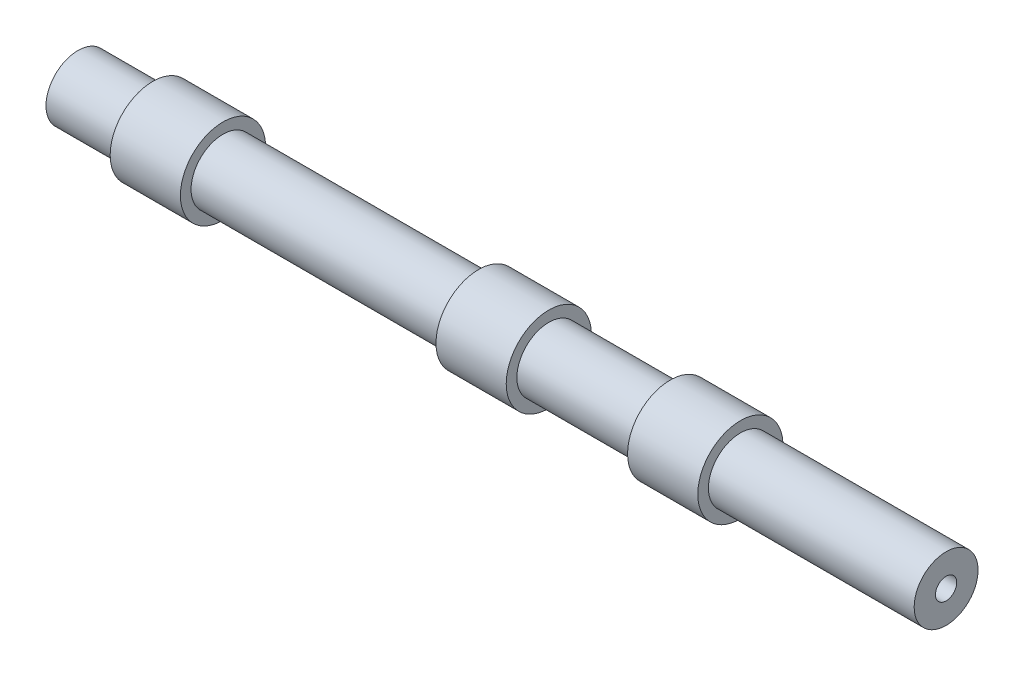
SolidWorks part; units mm, degrees
ref_plane "Front Plane" through (0, 0, 0) normal (0, 0, 1) x (1, 0, 0)
ref_plane "Top Plane" through (0, 0, 0) normal (0, 1, 0) x (1, 0, 0)
ref_plane "Right Plane" through (0, 0, 0) normal (1, 0, 0) x (0, 0, -1)
sketch "Sketch1" plane through (0, 0, 0) normal (0, 0, 1) x (1, 0, 0)
  line L0 (-102.2798, 0) -> (102.2798, 0) construction
  line L1 (-102.2798, 15) -> (-67.1503, 15)
  line L2 (-67.1503, 15) -> (-67.1503, 20)
  line L3 (-67.1503, 20) -> (-34.1803, 20)
  line L4 (-34.1803, 20) -> (-34.1803, 15)
  line L5 (-34.1803, 15) -> (85.8197, 15)
  line L6 (85.8197, 15) -> (85.8197, 20)
  line L7 (85.8197, 20) -> (118.7897, 20)
  line L8 (118.7897, 20) -> (118.7897, 15)
  line L9 (118.7897, 15) -> (175.7597, 15)
  line L10 (175.7597, 15) -> (175.7597, 20)
  line L11 (175.7597, 20) -> (208.7297, 20)
  line L12 (208.7297, 20) -> (208.7297, 15)
  line L13 (208.7297, 15) -> (218.2116, 15)
  line L14 (218.2116, 15) -> (305.3148, 15)
  point P4 (0, 0)
  dimension "D1" = 15
  dimension "D2" = 20
  dimension "D3" = 15
  dimension "D4" = 32.97
  dimension "D5" = 120
  dimension "D6" = 32.97
  dimension "D7" = 56.97
  dimension "D8" = 32.97
  dimension "D9" = 15
revolve "Revolve-Thin1" add sketch "Sketch1" angle 360 about L0
